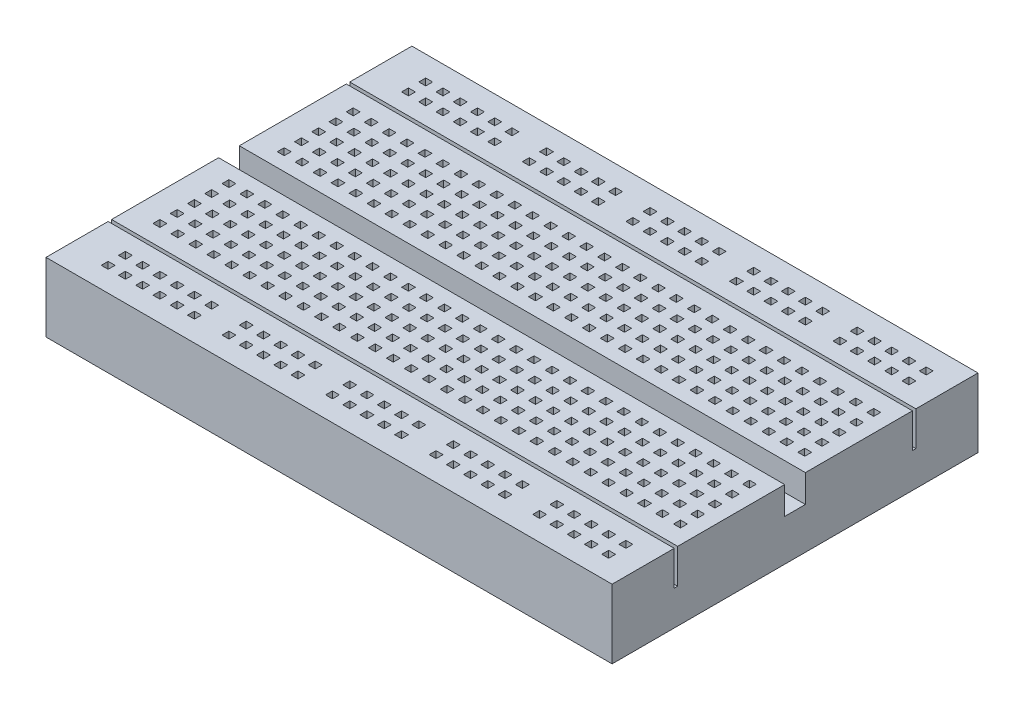
SolidWorks part; units mm, degrees
material "ABS"
ref_plane "Спереди" through (0, 0, 0) normal (0, 0, 1) x (1, 0, 0)
ref_plane "Сверху" through (0, 0, 0) normal (0, 1, 0) x (1, 0, 0)
ref_plane "Справа" through (0, 0, 0) normal (1, 0, 0) x (0, 0, -1)
sketch "Эскиз1" plane through (0, 0, 0) normal (0, 1, 0) x (1, 0, 0)
  line L1 (-41, 26.5) -> (41, 26.5)
  line L2 (-41, 26.5) -> (-41, -26.5)
  line L3 (-41, -26.5) -> (41, -26.5)
  line L4 (41, 26.5) -> (41, -26.5)
  line L5 (-41, 26.5) -> (41, -26.5) construction
  line L6 (-41, -26.5) -> (41, 26.5) construction
  point P0 (0, 0)
  dimension "D1" = 82
  dimension "D2" = 53
extrude "Бобышка-Вытянуть1" add sketch "Эскиз1" along normal blind 10
sketch "Эскиз2" plane through (0, 10, 0) normal (0, 1, 0) x (1, 0, 0)
  line L0 (41, -26.5) -> (41, 26.5) construction
  line L1 (-41, 1.5) -> (41, 1.5)
  line L2 (-41, 1.5) -> (-41, -1.5)
  line L3 (-41, -1.5) -> (41, -1.5)
  line L4 (41, 1.5) -> (41, -1.5)
  line L5 (-41, 1.5) -> (41, -1.5) construction
  line L6 (-41, -1.5) -> (41, 1.5) construction
  point P0 (0, 0)
  dimension "D1" = 3
extrude "Вырез-Вытянуть1" cut sketch "Эскиз2" against normal blind 4
sketch "Эскиз3" plane through (0, 10, 0) normal (0, 1, 0) x (1, 0, 0)
  line L0 (-41, -1.5) -> (-41, -26.5) construction
  line L1 (-36, -22.5) -> (-35, -22.5)
  line L2 (-36, -22.5) -> (-36, -23.5)
  line L3 (-36, -23.5) -> (-35, -23.5)
  line L4 (-35, -22.5) -> (-35, -23.5)
  line L5 (-41, -26.5) -> (41, -26.5) construction
  line L6 (-33.5, -22.5) -> (-32.5, -22.5)
  line L7 (-32.5, -22.5) -> (-32.5, -23.5)
  line L8 (-33.5, -23.5) -> (-32.5, -23.5)
  line L9 (-33.5, -22.5) -> (-33.5, -23.5)
  line L10 (-31, -22.5) -> (-30, -22.5)
  line L11 (-30, -22.5) -> (-30, -23.5)
  line L12 (-31, -23.5) -> (-30, -23.5)
  line L13 (-31, -22.5) -> (-31, -23.5)
  line L14 (-28.5, -22.5) -> (-27.5, -22.5)
  line L15 (-27.5, -22.5) -> (-27.5, -23.5)
  line L16 (-28.5, -23.5) -> (-27.5, -23.5)
  line L17 (-28.5, -22.5) -> (-28.5, -23.5)
  line L18 (-26, -22.5) -> (-25, -22.5)
  line L19 (-25, -22.5) -> (-25, -23.5)
  line L20 (-26, -23.5) -> (-25, -23.5)
  line L21 (-26, -22.5) -> (-26, -23.5)
  line L22 (-23.5, -22.5) -> (-22.5, -22.5)
  line L23 (-22.5, -22.5) -> (-22.5, -23.5)
  line L24 (-23.5, -23.5) -> (-22.5, -23.5)
  line L25 (-23.5, -22.5) -> (-23.5, -23.5)
  line L26 (-21, -22.5) -> (-20, -22.5) [skipped]
  line L27 (-20, -22.5) -> (-20, -23.5) [skipped]
  line L28 (-21, -23.5) -> (-20, -23.5) [skipped]
  line L29 (-21, -22.5) -> (-21, -23.5) [skipped]
  line L30 (-18.5, -22.5) -> (-17.5, -22.5)
  line L31 (-17.5, -22.5) -> (-17.5, -23.5)
  line L32 (-18.5, -23.5) -> (-17.5, -23.5)
  line L33 (-18.5, -22.5) -> (-18.5, -23.5)
  line L34 (-16, -22.5) -> (-15, -22.5)
  line L35 (-15, -22.5) -> (-15, -23.5)
  line L36 (-16, -23.5) -> (-15, -23.5)
  line L37 (-16, -22.5) -> (-16, -23.5)
  line L38 (-13.5, -22.5) -> (-12.5, -22.5)
  line L39 (-12.5, -22.5) -> (-12.5, -23.5)
  line L40 (-13.5, -23.5) -> (-12.5, -23.5)
  line L41 (-13.5, -22.5) -> (-13.5, -23.5)
  line L42 (-11, -22.5) -> (-10, -22.5)
  line L43 (-10, -22.5) -> (-10, -23.5)
  line L44 (-11, -23.5) -> (-10, -23.5)
  line L45 (-11, -22.5) -> (-11, -23.5)
  line L46 (-8.5, -22.5) -> (-7.5, -22.5)
  line L47 (-7.5, -22.5) -> (-7.5, -23.5)
  line L48 (-8.5, -23.5) -> (-7.5, -23.5)
  line L49 (-8.5, -22.5) -> (-8.5, -23.5)
  line L50 (-6, -22.5) -> (-5, -22.5) [skipped]
  line L51 (-5, -22.5) -> (-5, -23.5) [skipped]
  line L52 (-6, -23.5) -> (-5, -23.5) [skipped]
  line L53 (-6, -22.5) -> (-6, -23.5) [skipped]
  line L54 (-3.5, -22.5) -> (-2.5, -22.5)
  line L55 (-2.5, -22.5) -> (-2.5, -23.5)
  line L56 (-3.5, -23.5) -> (-2.5, -23.5)
  line L57 (-3.5, -22.5) -> (-3.5, -23.5)
  line L58 (-1, -22.5) -> (0, -22.5)
  line L59 (0, -22.5) -> (0, -23.5)
  line L60 (-1, -23.5) -> (0, -23.5)
  line L61 (-1, -22.5) -> (-1, -23.5)
  line L62 (1.5, -22.5) -> (2.5, -22.5)
  line L63 (2.5, -22.5) -> (2.5, -23.5)
  line L64 (1.5, -23.5) -> (2.5, -23.5)
  line L65 (1.5, -22.5) -> (1.5, -23.5)
  line L66 (4, -22.5) -> (5, -22.5)
  line L67 (5, -22.5) -> (5, -23.5)
  line L68 (4, -23.5) -> (5, -23.5)
  line L69 (4, -22.5) -> (4, -23.5)
  line L70 (6.5, -22.5) -> (7.5, -22.5)
  line L71 (7.5, -22.5) -> (7.5, -23.5)
  line L72 (6.5, -23.5) -> (7.5, -23.5)
  line L73 (6.5, -22.5) -> (6.5, -23.5)
  line L74 (9, -22.5) -> (10, -22.5) [skipped]
  line L75 (10, -22.5) -> (10, -23.5) [skipped]
  line L76 (9, -23.5) -> (10, -23.5) [skipped]
  line L77 (9, -22.5) -> (9, -23.5) [skipped]
  line L78 (11.5, -22.5) -> (12.5, -22.5)
  line L79 (12.5, -22.5) -> (12.5, -23.5)
  line L80 (11.5, -23.5) -> (12.5, -23.5)
  line L81 (11.5, -22.5) -> (11.5, -23.5)
  line L82 (14, -22.5) -> (15, -22.5)
  line L83 (15, -22.5) -> (15, -23.5)
  line L84 (14, -23.5) -> (15, -23.5)
  line L85 (14, -22.5) -> (14, -23.5)
  line L86 (16.5, -22.5) -> (17.5, -22.5)
  line L87 (17.5, -22.5) -> (17.5, -23.5)
  line L88 (16.5, -23.5) -> (17.5, -23.5)
  line L89 (16.5, -22.5) -> (16.5, -23.5)
  line L90 (19, -22.5) -> (20, -22.5)
  line L91 (20, -22.5) -> (20, -23.5)
  line L92 (19, -23.5) -> (20, -23.5)
  line L93 (19, -22.5) -> (19, -23.5)
  line L94 (21.5, -22.5) -> (22.5, -22.5)
  line L95 (22.5, -22.5) -> (22.5, -23.5)
  line L96 (21.5, -23.5) -> (22.5, -23.5)
  line L97 (21.5, -22.5) -> (21.5, -23.5)
  line L98 (24, -22.5) -> (25, -22.5) [skipped]
  line L99 (25, -22.5) -> (25, -23.5) [skipped]
  line L100 (24, -23.5) -> (25, -23.5) [skipped]
  line L101 (24, -22.5) -> (24, -23.5) [skipped]
  line L102 (26.5, -22.5) -> (27.5, -22.5)
  line L103 (27.5, -22.5) -> (27.5, -23.5)
  line L104 (26.5, -23.5) -> (27.5, -23.5)
  line L105 (26.5, -22.5) -> (26.5, -23.5)
  line L106 (29, -22.5) -> (30, -22.5)
  line L107 (30, -22.5) -> (30, -23.5)
  line L108 (29, -23.5) -> (30, -23.5)
  line L109 (29, -22.5) -> (29, -23.5)
  line L110 (31.5, -22.5) -> (32.5, -22.5)
  line L111 (32.5, -22.5) -> (32.5, -23.5)
  line L112 (31.5, -23.5) -> (32.5, -23.5)
  line L113 (31.5, -22.5) -> (31.5, -23.5)
  line L114 (34, -22.5) -> (35, -22.5)
  line L115 (35, -22.5) -> (35, -23.5)
  line L116 (34, -23.5) -> (35, -23.5)
  line L117 (34, -22.5) -> (34, -23.5)
  line L118 (36.5, -22.5) -> (37.5, -22.5)
  line L119 (37.5, -22.5) -> (37.5, -23.5)
  line L120 (36.5, -23.5) -> (37.5, -23.5)
  line L121 (36.5, -22.5) -> (36.5, -23.5)
  line L122 (-33.5, -20) -> (-32.5, -20)
  line L123 (-32.5, -20) -> (-32.5, -21)
  line L124 (-33.5, -21) -> (-32.5, -21)
  line L125 (-33.5, -20) -> (-33.5, -21)
  line L126 (-31, -20) -> (-30, -20)
  line L127 (-30, -20) -> (-30, -21)
  line L128 (-31, -21) -> (-30, -21)
  line L129 (-31, -20) -> (-31, -21)
  line L130 (-28.5, -20) -> (-27.5, -20)
  line L131 (-27.5, -20) -> (-27.5, -21)
  line L132 (-28.5, -21) -> (-27.5, -21)
  line L133 (-28.5, -20) -> (-28.5, -21)
  line L134 (-26, -20) -> (-25, -20)
  line L135 (-25, -20) -> (-25, -21)
  line L136 (-26, -21) -> (-25, -21)
  line L137 (-26, -20) -> (-26, -21)
  line L138 (-23.5, -20) -> (-22.5, -20)
  line L139 (-22.5, -20) -> (-22.5, -21)
  line L140 (-23.5, -21) -> (-22.5, -21)
  line L141 (-23.5, -20) -> (-23.5, -21)
  line L142 (-21, -20) -> (-20, -20) [skipped]
  line L143 (-20, -20) -> (-20, -21) [skipped]
  line L144 (-21, -21) -> (-20, -21) [skipped]
  line L145 (-21, -20) -> (-21, -21) [skipped]
  line L146 (-18.5, -20) -> (-17.5, -20)
  line L147 (-17.5, -20) -> (-17.5, -21)
  line L148 (-18.5, -21) -> (-17.5, -21)
  line L149 (-18.5, -20) -> (-18.5, -21)
  line L150 (-16, -20) -> (-15, -20)
  line L151 (-15, -20) -> (-15, -21)
  line L152 (-16, -21) -> (-15, -21)
  line L153 (-16, -20) -> (-16, -21)
  line L154 (-13.5, -20) -> (-12.5, -20)
  line L155 (-12.5, -20) -> (-12.5, -21)
  line L156 (-13.5, -21) -> (-12.5, -21)
  line L157 (-13.5, -20) -> (-13.5, -21)
  line L158 (-11, -20) -> (-10, -20)
  line L159 (-10, -20) -> (-10, -21)
  line L160 (-11, -21) -> (-10, -21)
  line L161 (-11, -20) -> (-11, -21)
  line L162 (-8.5, -20) -> (-7.5, -20)
  line L163 (-7.5, -20) -> (-7.5, -21)
  line L164 (-8.5, -21) -> (-7.5, -21)
  line L165 (-8.5, -20) -> (-8.5, -21)
  line L166 (-6, -20) -> (-5, -20) [skipped]
  line L167 (-5, -20) -> (-5, -21) [skipped]
  line L168 (-6, -21) -> (-5, -21) [skipped]
  line L169 (-6, -20) -> (-6, -21) [skipped]
  line L170 (-3.5, -20) -> (-2.5, -20)
  line L171 (-2.5, -20) -> (-2.5, -21)
  line L172 (-3.5, -21) -> (-2.5, -21)
  line L173 (-3.5, -20) -> (-3.5, -21)
  line L174 (-1, -20) -> (0, -20)
  line L175 (0, -20) -> (0, -21)
  line L176 (-1, -21) -> (0, -21)
  line L177 (-1, -20) -> (-1, -21)
  line L178 (1.5, -20) -> (2.5, -20)
  line L179 (2.5, -20) -> (2.5, -21)
  line L180 (1.5, -21) -> (2.5, -21)
  line L181 (1.5, -20) -> (1.5, -21)
  line L182 (4, -20) -> (5, -20)
  line L183 (5, -20) -> (5, -21)
  line L184 (4, -21) -> (5, -21)
  line L185 (4, -20) -> (4, -21)
  line L186 (6.5, -20) -> (7.5, -20)
  line L187 (7.5, -20) -> (7.5, -21)
  line L188 (6.5, -21) -> (7.5, -21)
  line L189 (6.5, -20) -> (6.5, -21)
  line L190 (9, -20) -> (10, -20) [skipped]
  line L191 (10, -20) -> (10, -21) [skipped]
  line L192 (9, -21) -> (10, -21) [skipped]
  line L193 (9, -20) -> (9, -21) [skipped]
  line L194 (11.5, -20) -> (12.5, -20)
  line L195 (12.5, -20) -> (12.5, -21)
  line L196 (11.5, -21) -> (12.5, -21)
  line L197 (11.5, -20) -> (11.5, -21)
  line L198 (14, -20) -> (15, -20)
  line L199 (15, -20) -> (15, -21)
  line L200 (14, -21) -> (15, -21)
  line L201 (14, -20) -> (14, -21)
  line L202 (16.5, -20) -> (17.5, -20)
  line L203 (17.5, -20) -> (17.5, -21)
  line L204 (16.5, -21) -> (17.5, -21)
  line L205 (16.5, -20) -> (16.5, -21)
  line L206 (19, -20) -> (20, -20)
  line L207 (20, -20) -> (20, -21)
  line L208 (19, -21) -> (20, -21)
  line L209 (19, -20) -> (19, -21)
  line L210 (21.5, -20) -> (22.5, -20)
  line L211 (22.5, -20) -> (22.5, -21)
  line L212 (21.5, -21) -> (22.5, -21)
  line L213 (21.5, -20) -> (21.5, -21)
  line L214 (24, -20) -> (25, -20) [skipped]
  line L215 (25, -20) -> (25, -21) [skipped]
  line L216 (24, -21) -> (25, -21) [skipped]
  line L217 (24, -20) -> (24, -21) [skipped]
  line L218 (26.5, -20) -> (27.5, -20)
  line L219 (27.5, -20) -> (27.5, -21)
  line L220 (26.5, -21) -> (27.5, -21)
  line L221 (26.5, -20) -> (26.5, -21)
  line L222 (29, -20) -> (30, -20)
  line L223 (30, -20) -> (30, -21)
  line L224 (29, -21) -> (30, -21)
  line L225 (29, -20) -> (29, -21)
  line L226 (31.5, -20) -> (32.5, -20)
  line L227 (32.5, -20) -> (32.5, -21)
  line L228 (31.5, -21) -> (32.5, -21)
  line L229 (31.5, -20) -> (31.5, -21)
  line L230 (34, -20) -> (35, -20)
  line L231 (35, -20) -> (35, -21)
  line L232 (34, -21) -> (35, -21)
  line L233 (34, -20) -> (34, -21)
  line L234 (36.5, -20) -> (37.5, -20)
  line L235 (37.5, -20) -> (37.5, -21)
  line L236 (36.5, -21) -> (37.5, -21)
  line L237 (36.5, -20) -> (36.5, -21)
  line L238 (-36, -20) -> (-35, -20)
  line L239 (-35, -20) -> (-35, -21)
  line L240 (-36, -21) -> (-35, -21)
  line L241 (-36, -20) -> (-36, -21)
  dimension "D1" = 1
  dimension "D2" = 1
  dimension "D3" = 5
  dimension "D4" = 3
  dimension "D5" = 30
  dimension "D6" = 2
extrude "Вырез-Вытянуть2" cut sketch "Эскиз3" against normal blind 5
sketch "Эскиз4" plane through (0, 10, 0) normal (0, 1, 0) x (1, 0, 0)
  line L0 (-36, -21) -> (-35, -21) construction
  line L1 (-37.5, -13.5) -> (-36.5, -13.5)
  line L2 (-37.5, -13.5) -> (-37.5, -14.5)
  line L3 (-37.5, -14.5) -> (-36.5, -14.5)
  line L4 (-36.5, -13.5) -> (-36.5, -14.5)
  line L5 (-35, -21) -> (-35, -20) construction
  line L6 (-41, -1.5) -> (-41, -26.5) construction
  line L7 (-35, -20) -> (-36, -20) construction
  line L8 (-36, -23.5) -> (-35, -23.5) construction
  line L9 (-41, -26.5) -> (41, -26.5) construction
  line L10 (-34.9, -13.5) -> (-33.9, -13.5)
  line L11 (-33.9, -13.5) -> (-33.9, -14.5)
  line L12 (-34.9, -13.5) -> (-34.9, -14.5)
  line L13 (-34.9, -14.5) -> (-33.9, -14.5)
  line L14 (-32.3, -13.5) -> (-31.3, -13.5)
  line L15 (-31.3, -13.5) -> (-31.3, -14.5)
  line L16 (-32.3, -13.5) -> (-32.3, -14.5)
  line L17 (-32.3, -14.5) -> (-31.3, -14.5)
  line L18 (-29.7, -13.5) -> (-28.7, -13.5)
  line L19 (-28.7, -13.5) -> (-28.7, -14.5)
  line L20 (-29.7, -13.5) -> (-29.7, -14.5)
  line L21 (-29.7, -14.5) -> (-28.7, -14.5)
  line L22 (-27.1, -13.5) -> (-26.1, -13.5)
  line L23 (-26.1, -13.5) -> (-26.1, -14.5)
  line L24 (-27.1, -13.5) -> (-27.1, -14.5)
  line L25 (-27.1, -14.5) -> (-26.1, -14.5)
  line L26 (-24.5, -13.5) -> (-23.5, -13.5)
  line L27 (-23.5, -13.5) -> (-23.5, -14.5)
  line L28 (-24.5, -13.5) -> (-24.5, -14.5)
  line L29 (-24.5, -14.5) -> (-23.5, -14.5)
  line L30 (-21.9, -13.5) -> (-20.9, -13.5)
  line L31 (-20.9, -13.5) -> (-20.9, -14.5)
  line L32 (-21.9, -13.5) -> (-21.9, -14.5)
  line L33 (-21.9, -14.5) -> (-20.9, -14.5)
  line L34 (-19.3, -13.5) -> (-18.3, -13.5)
  line L35 (-18.3, -13.5) -> (-18.3, -14.5)
  line L36 (-19.3, -13.5) -> (-19.3, -14.5)
  line L37 (-19.3, -14.5) -> (-18.3, -14.5)
  line L38 (-16.7, -13.5) -> (-15.7, -13.5)
  line L39 (-15.7, -13.5) -> (-15.7, -14.5)
  line L40 (-16.7, -13.5) -> (-16.7, -14.5)
  line L41 (-16.7, -14.5) -> (-15.7, -14.5)
  line L42 (-14.1, -13.5) -> (-13.1, -13.5)
  line L43 (-13.1, -13.5) -> (-13.1, -14.5)
  line L44 (-14.1, -13.5) -> (-14.1, -14.5)
  line L45 (-14.1, -14.5) -> (-13.1, -14.5)
  line L46 (-11.5, -13.5) -> (-10.5, -13.5)
  line L47 (-10.5, -13.5) -> (-10.5, -14.5)
  line L48 (-11.5, -13.5) -> (-11.5, -14.5)
  line L49 (-11.5, -14.5) -> (-10.5, -14.5)
  line L50 (-8.9, -13.5) -> (-7.9, -13.5)
  line L51 (-7.9, -13.5) -> (-7.9, -14.5)
  line L52 (-8.9, -13.5) -> (-8.9, -14.5)
  line L53 (-8.9, -14.5) -> (-7.9, -14.5)
  line L54 (-6.3, -13.5) -> (-5.3, -13.5)
  line L55 (-5.3, -13.5) -> (-5.3, -14.5)
  line L56 (-6.3, -13.5) -> (-6.3, -14.5)
  line L57 (-6.3, -14.5) -> (-5.3, -14.5)
  line L58 (-3.7, -13.5) -> (-2.7, -13.5)
  line L59 (-2.7, -13.5) -> (-2.7, -14.5)
  line L60 (-3.7, -13.5) -> (-3.7, -14.5)
  line L61 (-3.7, -14.5) -> (-2.7, -14.5)
  line L62 (-1.1, -13.5) -> (-0.1, -13.5)
  line L63 (-0.1, -13.5) -> (-0.1, -14.5)
  line L64 (-1.1, -13.5) -> (-1.1, -14.5)
  line L65 (-1.1, -14.5) -> (-0.1, -14.5)
  line L66 (1.5, -13.5) -> (2.5, -13.5)
  line L67 (2.5, -13.5) -> (2.5, -14.5)
  line L68 (1.5, -13.5) -> (1.5, -14.5)
  line L69 (1.5, -14.5) -> (2.5, -14.5)
  line L70 (4.1, -13.5) -> (5.1, -13.5)
  line L71 (5.1, -13.5) -> (5.1, -14.5)
  line L72 (4.1, -13.5) -> (4.1, -14.5)
  line L73 (4.1, -14.5) -> (5.1, -14.5)
  line L74 (6.7, -13.5) -> (7.7, -13.5)
  line L75 (7.7, -13.5) -> (7.7, -14.5)
  line L76 (6.7, -13.5) -> (6.7, -14.5)
  line L77 (6.7, -14.5) -> (7.7, -14.5)
  line L78 (9.3, -13.5) -> (10.3, -13.5)
  line L79 (10.3, -13.5) -> (10.3, -14.5)
  line L80 (9.3, -13.5) -> (9.3, -14.5)
  line L81 (9.3, -14.5) -> (10.3, -14.5)
  line L82 (11.9, -13.5) -> (12.9, -13.5)
  line L83 (12.9, -13.5) -> (12.9, -14.5)
  line L84 (11.9, -13.5) -> (11.9, -14.5)
  line L85 (11.9, -14.5) -> (12.9, -14.5)
  line L86 (14.5, -13.5) -> (15.5, -13.5)
  line L87 (15.5, -13.5) -> (15.5, -14.5)
  line L88 (14.5, -13.5) -> (14.5, -14.5)
  line L89 (14.5, -14.5) -> (15.5, -14.5)
  line L90 (17.1, -13.5) -> (18.1, -13.5)
  line L91 (18.1, -13.5) -> (18.1, -14.5)
  line L92 (17.1, -13.5) -> (17.1, -14.5)
  line L93 (17.1, -14.5) -> (18.1, -14.5)
  line L94 (19.7, -13.5) -> (20.7, -13.5)
  line L95 (20.7, -13.5) -> (20.7, -14.5)
  line L96 (19.7, -13.5) -> (19.7, -14.5)
  line L97 (19.7, -14.5) -> (20.7, -14.5)
  line L98 (22.3, -13.5) -> (23.3, -13.5)
  line L99 (23.3, -13.5) -> (23.3, -14.5)
  line L100 (22.3, -13.5) -> (22.3, -14.5)
  line L101 (22.3, -14.5) -> (23.3, -14.5)
  line L102 (24.9, -13.5) -> (25.9, -13.5)
  line L103 (25.9, -13.5) -> (25.9, -14.5)
  line L104 (24.9, -13.5) -> (24.9, -14.5)
  line L105 (24.9, -14.5) -> (25.9, -14.5)
  line L106 (27.5, -13.5) -> (28.5, -13.5)
  line L107 (28.5, -13.5) -> (28.5, -14.5)
  line L108 (27.5, -13.5) -> (27.5, -14.5)
  line L109 (27.5, -14.5) -> (28.5, -14.5)
  line L110 (30.1, -13.5) -> (31.1, -13.5)
  line L111 (31.1, -13.5) -> (31.1, -14.5)
  line L112 (30.1, -13.5) -> (30.1, -14.5)
  line L113 (30.1, -14.5) -> (31.1, -14.5)
  line L114 (32.7, -13.5) -> (33.7, -13.5)
  line L115 (33.7, -13.5) -> (33.7, -14.5)
  line L116 (32.7, -13.5) -> (32.7, -14.5)
  line L117 (32.7, -14.5) -> (33.7, -14.5)
  line L118 (35.3, -13.5) -> (36.3, -13.5)
  line L119 (36.3, -13.5) -> (36.3, -14.5)
  line L120 (35.3, -13.5) -> (35.3, -14.5)
  line L121 (35.3, -14.5) -> (36.3, -14.5)
  line L122 (37.9, -13.5) -> (38.9, -13.5)
  line L123 (38.9, -13.5) -> (38.9, -14.5)
  line L124 (37.9, -13.5) -> (37.9, -14.5)
  line L125 (37.9, -14.5) -> (38.9, -14.5)
  line L126 (-34.9, -11) -> (-33.9, -11)
  line L127 (-33.9, -11) -> (-33.9, -12)
  line L128 (-34.9, -11) -> (-34.9, -12)
  line L129 (-34.9, -12) -> (-33.9, -12)
  line L130 (-32.3, -11) -> (-31.3, -11)
  line L131 (-31.3, -11) -> (-31.3, -12)
  line L132 (-32.3, -11) -> (-32.3, -12)
  line L133 (-32.3, -12) -> (-31.3, -12)
  line L134 (-29.7, -11) -> (-28.7, -11)
  line L135 (-28.7, -11) -> (-28.7, -12)
  line L136 (-29.7, -11) -> (-29.7, -12)
  line L137 (-29.7, -12) -> (-28.7, -12)
  line L138 (-27.1, -11) -> (-26.1, -11)
  line L139 (-26.1, -11) -> (-26.1, -12)
  line L140 (-27.1, -11) -> (-27.1, -12)
  line L141 (-27.1, -12) -> (-26.1, -12)
  line L142 (-24.5, -11) -> (-23.5, -11)
  line L143 (-23.5, -11) -> (-23.5, -12)
  line L144 (-24.5, -11) -> (-24.5, -12)
  line L145 (-24.5, -12) -> (-23.5, -12)
  line L146 (-21.9, -11) -> (-20.9, -11)
  line L147 (-20.9, -11) -> (-20.9, -12)
  line L148 (-21.9, -11) -> (-21.9, -12)
  line L149 (-21.9, -12) -> (-20.9, -12)
  line L150 (-19.3, -11) -> (-18.3, -11)
  line L151 (-18.3, -11) -> (-18.3, -12)
  line L152 (-19.3, -11) -> (-19.3, -12)
  line L153 (-19.3, -12) -> (-18.3, -12)
  line L154 (-16.7, -11) -> (-15.7, -11)
  line L155 (-15.7, -11) -> (-15.7, -12)
  line L156 (-16.7, -11) -> (-16.7, -12)
  line L157 (-16.7, -12) -> (-15.7, -12)
  line L158 (-14.1, -11) -> (-13.1, -11)
  line L159 (-13.1, -11) -> (-13.1, -12)
  line L160 (-14.1, -11) -> (-14.1, -12)
  line L161 (-14.1, -12) -> (-13.1, -12)
  line L162 (-11.5, -11) -> (-10.5, -11)
  line L163 (-10.5, -11) -> (-10.5, -12)
  line L164 (-11.5, -11) -> (-11.5, -12)
  line L165 (-11.5, -12) -> (-10.5, -12)
  line L166 (-8.9, -11) -> (-7.9, -11)
  line L167 (-7.9, -11) -> (-7.9, -12)
  line L168 (-8.9, -11) -> (-8.9, -12)
  line L169 (-8.9, -12) -> (-7.9, -12)
  line L170 (-6.3, -11) -> (-5.3, -11)
  line L171 (-5.3, -11) -> (-5.3, -12)
  line L172 (-6.3, -11) -> (-6.3, -12)
  line L173 (-6.3, -12) -> (-5.3, -12)
  line L174 (-3.7, -11) -> (-2.7, -11)
  line L175 (-2.7, -11) -> (-2.7, -12)
  line L176 (-3.7, -11) -> (-3.7, -12)
  line L177 (-3.7, -12) -> (-2.7, -12)
  line L178 (-1.1, -11) -> (-0.1, -11)
  line L179 (-0.1, -11) -> (-0.1, -12)
  line L180 (-1.1, -11) -> (-1.1, -12)
  line L181 (-1.1, -12) -> (-0.1, -12)
  line L182 (1.5, -11) -> (2.5, -11)
  line L183 (2.5, -11) -> (2.5, -12)
  line L184 (1.5, -11) -> (1.5, -12)
  line L185 (1.5, -12) -> (2.5, -12)
  line L186 (4.1, -11) -> (5.1, -11)
  line L187 (5.1, -11) -> (5.1, -12)
  line L188 (4.1, -11) -> (4.1, -12)
  line L189 (4.1, -12) -> (5.1, -12)
  line L190 (6.7, -11) -> (7.7, -11)
  line L191 (7.7, -11) -> (7.7, -12)
  line L192 (6.7, -11) -> (6.7, -12)
  line L193 (6.7, -12) -> (7.7, -12)
  line L194 (9.3, -11) -> (10.3, -11)
  line L195 (10.3, -11) -> (10.3, -12)
  line L196 (9.3, -11) -> (9.3, -12)
  line L197 (9.3, -12) -> (10.3, -12)
  line L198 (11.9, -11) -> (12.9, -11)
  line L199 (12.9, -11) -> (12.9, -12)
  line L200 (11.9, -11) -> (11.9, -12)
  line L201 (11.9, -12) -> (12.9, -12)
  line L202 (14.5, -11) -> (15.5, -11)
  line L203 (15.5, -11) -> (15.5, -12)
  line L204 (14.5, -11) -> (14.5, -12)
  line L205 (14.5, -12) -> (15.5, -12)
  line L206 (17.1, -11) -> (18.1, -11)
  line L207 (18.1, -11) -> (18.1, -12)
  line L208 (17.1, -11) -> (17.1, -12)
  line L209 (17.1, -12) -> (18.1, -12)
  line L210 (19.7, -11) -> (20.7, -11)
  line L211 (20.7, -11) -> (20.7, -12)
  line L212 (19.7, -11) -> (19.7, -12)
  line L213 (19.7, -12) -> (20.7, -12)
  line L214 (22.3, -11) -> (23.3, -11)
  line L215 (23.3, -11) -> (23.3, -12)
  line L216 (22.3, -11) -> (22.3, -12)
  line L217 (22.3, -12) -> (23.3, -12)
  line L218 (24.9, -11) -> (25.9, -11)
  line L219 (25.9, -11) -> (25.9, -12)
  line L220 (24.9, -11) -> (24.9, -12)
  line L221 (24.9, -12) -> (25.9, -12)
  line L222 (27.5, -11) -> (28.5, -11)
  line L223 (28.5, -11) -> (28.5, -12)
  line L224 (27.5, -11) -> (27.5, -12)
  line L225 (27.5, -12) -> (28.5, -12)
  line L226 (30.1, -11) -> (31.1, -11)
  line L227 (31.1, -11) -> (31.1, -12)
  line L228 (30.1, -11) -> (30.1, -12)
  line L229 (30.1, -12) -> (31.1, -12)
  line L230 (32.7, -11) -> (33.7, -11)
  line L231 (33.7, -11) -> (33.7, -12)
  line L232 (32.7, -11) -> (32.7, -12)
  line L233 (32.7, -12) -> (33.7, -12)
  line L234 (35.3, -11) -> (36.3, -11)
  line L235 (36.3, -11) -> (36.3, -12)
  line L236 (35.3, -11) -> (35.3, -12)
  line L237 (35.3, -12) -> (36.3, -12)
  line L238 (37.9, -11) -> (38.9, -11)
  line L239 (38.9, -11) -> (38.9, -12)
  line L240 (37.9, -11) -> (37.9, -12)
  line L241 (37.9, -12) -> (38.9, -12)
  line L242 (-34.9, -8.5) -> (-33.9, -8.5)
  line L243 (-33.9, -8.5) -> (-33.9, -9.5)
  line L244 (-34.9, -8.5) -> (-34.9, -9.5)
  line L245 (-34.9, -9.5) -> (-33.9, -9.5)
  line L246 (-32.3, -8.5) -> (-31.3, -8.5)
  line L247 (-31.3, -8.5) -> (-31.3, -9.5)
  line L248 (-32.3, -8.5) -> (-32.3, -9.5)
  line L249 (-32.3, -9.5) -> (-31.3, -9.5)
  line L250 (-29.7, -8.5) -> (-28.7, -8.5)
  line L251 (-28.7, -8.5) -> (-28.7, -9.5)
  line L252 (-29.7, -8.5) -> (-29.7, -9.5)
  line L253 (-29.7, -9.5) -> (-28.7, -9.5)
  line L254 (-27.1, -8.5) -> (-26.1, -8.5)
  line L255 (-26.1, -8.5) -> (-26.1, -9.5)
  line L256 (-27.1, -8.5) -> (-27.1, -9.5)
  line L257 (-27.1, -9.5) -> (-26.1, -9.5)
  line L258 (-24.5, -8.5) -> (-23.5, -8.5)
  line L259 (-23.5, -8.5) -> (-23.5, -9.5)
  line L260 (-24.5, -8.5) -> (-24.5, -9.5)
  line L261 (-24.5, -9.5) -> (-23.5, -9.5)
  line L262 (-21.9, -8.5) -> (-20.9, -8.5)
  line L263 (-20.9, -8.5) -> (-20.9, -9.5)
  line L264 (-21.9, -8.5) -> (-21.9, -9.5)
  line L265 (-21.9, -9.5) -> (-20.9, -9.5)
  line L266 (-19.3, -8.5) -> (-18.3, -8.5)
  line L267 (-18.3, -8.5) -> (-18.3, -9.5)
  line L268 (-19.3, -8.5) -> (-19.3, -9.5)
  line L269 (-19.3, -9.5) -> (-18.3, -9.5)
  line L270 (-16.7, -8.5) -> (-15.7, -8.5)
  line L271 (-15.7, -8.5) -> (-15.7, -9.5)
  line L272 (-16.7, -8.5) -> (-16.7, -9.5)
  line L273 (-16.7, -9.5) -> (-15.7, -9.5)
  line L274 (-14.1, -8.5) -> (-13.1, -8.5)
  line L275 (-13.1, -8.5) -> (-13.1, -9.5)
  line L276 (-14.1, -8.5) -> (-14.1, -9.5)
  line L277 (-14.1, -9.5) -> (-13.1, -9.5)
  line L278 (-11.5, -8.5) -> (-10.5, -8.5)
  line L279 (-10.5, -8.5) -> (-10.5, -9.5)
  line L280 (-11.5, -8.5) -> (-11.5, -9.5)
  line L281 (-11.5, -9.5) -> (-10.5, -9.5)
  line L282 (-8.9, -8.5) -> (-7.9, -8.5)
  line L283 (-7.9, -8.5) -> (-7.9, -9.5)
  line L284 (-8.9, -8.5) -> (-8.9, -9.5)
  line L285 (-8.9, -9.5) -> (-7.9, -9.5)
  line L286 (-6.3, -8.5) -> (-5.3, -8.5)
  line L287 (-5.3, -8.5) -> (-5.3, -9.5)
  line L288 (-6.3, -8.5) -> (-6.3, -9.5)
  line L289 (-6.3, -9.5) -> (-5.3, -9.5)
  line L290 (-3.7, -8.5) -> (-2.7, -8.5)
  line L291 (-2.7, -8.5) -> (-2.7, -9.5)
  line L292 (-3.7, -8.5) -> (-3.7, -9.5)
  line L293 (-3.7, -9.5) -> (-2.7, -9.5)
  line L294 (-1.1, -8.5) -> (-0.1, -8.5)
  line L295 (-0.1, -8.5) -> (-0.1, -9.5)
  line L296 (-1.1, -8.5) -> (-1.1, -9.5)
  line L297 (-1.1, -9.5) -> (-0.1, -9.5)
  line L298 (1.5, -8.5) -> (2.5, -8.5)
  line L299 (2.5, -8.5) -> (2.5, -9.5)
  line L300 (1.5, -8.5) -> (1.5, -9.5)
  line L301 (1.5, -9.5) -> (2.5, -9.5)
  line L302 (4.1, -8.5) -> (5.1, -8.5)
  line L303 (5.1, -8.5) -> (5.1, -9.5)
  line L304 (4.1, -8.5) -> (4.1, -9.5)
  line L305 (4.1, -9.5) -> (5.1, -9.5)
  line L306 (6.7, -8.5) -> (7.7, -8.5)
  line L307 (7.7, -8.5) -> (7.7, -9.5)
  line L308 (6.7, -8.5) -> (6.7, -9.5)
  line L309 (6.7, -9.5) -> (7.7, -9.5)
  line L310 (9.3, -8.5) -> (10.3, -8.5)
  line L311 (10.3, -8.5) -> (10.3, -9.5)
  line L312 (9.3, -8.5) -> (9.3, -9.5)
  line L313 (9.3, -9.5) -> (10.3, -9.5)
  line L314 (11.9, -8.5) -> (12.9, -8.5)
  line L315 (12.9, -8.5) -> (12.9, -9.5)
  line L316 (11.9, -8.5) -> (11.9, -9.5)
  line L317 (11.9, -9.5) -> (12.9, -9.5)
  line L318 (14.5, -8.5) -> (15.5, -8.5)
  line L319 (15.5, -8.5) -> (15.5, -9.5)
  line L320 (14.5, -8.5) -> (14.5, -9.5)
  line L321 (14.5, -9.5) -> (15.5, -9.5)
  line L322 (17.1, -8.5) -> (18.1, -8.5)
  line L323 (18.1, -8.5) -> (18.1, -9.5)
  line L324 (17.1, -8.5) -> (17.1, -9.5)
  line L325 (17.1, -9.5) -> (18.1, -9.5)
  line L326 (19.7, -8.5) -> (20.7, -8.5)
  line L327 (20.7, -8.5) -> (20.7, -9.5)
  line L328 (19.7, -8.5) -> (19.7, -9.5)
  line L329 (19.7, -9.5) -> (20.7, -9.5)
  line L330 (22.3, -8.5) -> (23.3, -8.5)
  line L331 (23.3, -8.5) -> (23.3, -9.5)
  line L332 (22.3, -8.5) -> (22.3, -9.5)
  line L333 (22.3, -9.5) -> (23.3, -9.5)
  line L334 (24.9, -8.5) -> (25.9, -8.5)
  line L335 (25.9, -8.5) -> (25.9, -9.5)
  line L336 (24.9, -8.5) -> (24.9, -9.5)
  line L337 (24.9, -9.5) -> (25.9, -9.5)
  line L338 (27.5, -8.5) -> (28.5, -8.5)
  line L339 (28.5, -8.5) -> (28.5, -9.5)
  line L340 (27.5, -8.5) -> (27.5, -9.5)
  line L341 (27.5, -9.5) -> (28.5, -9.5)
  line L342 (30.1, -8.5) -> (31.1, -8.5)
  line L343 (31.1, -8.5) -> (31.1, -9.5)
  line L344 (30.1, -8.5) -> (30.1, -9.5)
  line L345 (30.1, -9.5) -> (31.1, -9.5)
  line L346 (32.7, -8.5) -> (33.7, -8.5)
  line L347 (33.7, -8.5) -> (33.7, -9.5)
  line L348 (32.7, -8.5) -> (32.7, -9.5)
  line L349 (32.7, -9.5) -> (33.7, -9.5)
  line L350 (35.3, -8.5) -> (36.3, -8.5)
  line L351 (36.3, -8.5) -> (36.3, -9.5)
  line L352 (35.3, -8.5) -> (35.3, -9.5)
  line L353 (35.3, -9.5) -> (36.3, -9.5)
  line L354 (37.9, -8.5) -> (38.9, -8.5)
  line L355 (38.9, -8.5) -> (38.9, -9.5)
  line L356 (37.9, -8.5) -> (37.9, -9.5)
  line L357 (37.9, -9.5) -> (38.9, -9.5)
  line L358 (-34.9, -6) -> (-33.9, -6)
  line L359 (-33.9, -6) -> (-33.9, -7)
  line L360 (-34.9, -6) -> (-34.9, -7)
  line L361 (-34.9, -7) -> (-33.9, -7)
  line L362 (-32.3, -6) -> (-31.3, -6)
  line L363 (-31.3, -6) -> (-31.3, -7)
  line L364 (-32.3, -6) -> (-32.3, -7)
  line L365 (-32.3, -7) -> (-31.3, -7)
  line L366 (-29.7, -6) -> (-28.7, -6)
  line L367 (-28.7, -6) -> (-28.7, -7)
  line L368 (-29.7, -6) -> (-29.7, -7)
  line L369 (-29.7, -7) -> (-28.7, -7)
  line L370 (-27.1, -6) -> (-26.1, -6)
  line L371 (-26.1, -6) -> (-26.1, -7)
  line L372 (-27.1, -6) -> (-27.1, -7)
  line L373 (-27.1, -7) -> (-26.1, -7)
  line L374 (-24.5, -6) -> (-23.5, -6)
  line L375 (-23.5, -6) -> (-23.5, -7)
  line L376 (-24.5, -6) -> (-24.5, -7)
  line L377 (-24.5, -7) -> (-23.5, -7)
  line L378 (-21.9, -6) -> (-20.9, -6)
  line L379 (-20.9, -6) -> (-20.9, -7)
  line L380 (-21.9, -6) -> (-21.9, -7)
  line L381 (-21.9, -7) -> (-20.9, -7)
  line L382 (-19.3, -6) -> (-18.3, -6)
  line L383 (-18.3, -6) -> (-18.3, -7)
  line L384 (-19.3, -6) -> (-19.3, -7)
  line L385 (-19.3, -7) -> (-18.3, -7)
  line L386 (-16.7, -6) -> (-15.7, -6)
  line L387 (-15.7, -6) -> (-15.7, -7)
  line L388 (-16.7, -6) -> (-16.7, -7)
  line L389 (-16.7, -7) -> (-15.7, -7)
  line L390 (-14.1, -6) -> (-13.1, -6)
  line L391 (-13.1, -6) -> (-13.1, -7)
  line L392 (-14.1, -6) -> (-14.1, -7)
  line L393 (-14.1, -7) -> (-13.1, -7)
  line L394 (-11.5, -6) -> (-10.5, -6)
  line L395 (-10.5, -6) -> (-10.5, -7)
  line L396 (-11.5, -6) -> (-11.5, -7)
  line L397 (-11.5, -7) -> (-10.5, -7)
  line L398 (-8.9, -6) -> (-7.9, -6)
  line L399 (-7.9, -6) -> (-7.9, -7)
  line L400 (-8.9, -6) -> (-8.9, -7)
  line L401 (-8.9, -7) -> (-7.9, -7)
  line L402 (-6.3, -6) -> (-5.3, -6)
  line L403 (-5.3, -6) -> (-5.3, -7)
  line L404 (-6.3, -6) -> (-6.3, -7)
  line L405 (-6.3, -7) -> (-5.3, -7)
  line L406 (-3.7, -6) -> (-2.7, -6)
  line L407 (-2.7, -6) -> (-2.7, -7)
  line L408 (-3.7, -6) -> (-3.7, -7)
  line L409 (-3.7, -7) -> (-2.7, -7)
  line L410 (-1.1, -6) -> (-0.1, -6)
  line L411 (-0.1, -6) -> (-0.1, -7)
  line L412 (-1.1, -6) -> (-1.1, -7)
  line L413 (-1.1, -7) -> (-0.1, -7)
  line L414 (1.5, -6) -> (2.5, -6)
  line L415 (2.5, -6) -> (2.5, -7)
  line L416 (1.5, -6) -> (1.5, -7)
  line L417 (1.5, -7) -> (2.5, -7)
  line L418 (4.1, -6) -> (5.1, -6)
  line L419 (5.1, -6) -> (5.1, -7)
  line L420 (4.1, -6) -> (4.1, -7)
  line L421 (4.1, -7) -> (5.1, -7)
  line L422 (6.7, -6) -> (7.7, -6)
  line L423 (7.7, -6) -> (7.7, -7)
  line L424 (6.7, -6) -> (6.7, -7)
  line L425 (6.7, -7) -> (7.7, -7)
  line L426 (9.3, -6) -> (10.3, -6)
  line L427 (10.3, -6) -> (10.3, -7)
  line L428 (9.3, -6) -> (9.3, -7)
  line L429 (9.3, -7) -> (10.3, -7)
  line L430 (11.9, -6) -> (12.9, -6)
  line L431 (12.9, -6) -> (12.9, -7)
  line L432 (11.9, -6) -> (11.9, -7)
  line L433 (11.9, -7) -> (12.9, -7)
  line L434 (14.5, -6) -> (15.5, -6)
  line L435 (15.5, -6) -> (15.5, -7)
  line L436 (14.5, -6) -> (14.5, -7)
  line L437 (14.5, -7) -> (15.5, -7)
  line L438 (17.1, -6) -> (18.1, -6)
  line L439 (18.1, -6) -> (18.1, -7)
  line L440 (17.1, -6) -> (17.1, -7)
  line L441 (17.1, -7) -> (18.1, -7)
  line L442 (19.7, -6) -> (20.7, -6)
  line L443 (20.7, -6) -> (20.7, -7)
  line L444 (19.7, -6) -> (19.7, -7)
  line L445 (19.7, -7) -> (20.7, -7)
  line L446 (22.3, -6) -> (23.3, -6)
  line L447 (23.3, -6) -> (23.3, -7)
  line L448 (22.3, -6) -> (22.3, -7)
  line L449 (22.3, -7) -> (23.3, -7)
  line L450 (24.9, -6) -> (25.9, -6)
  line L451 (25.9, -6) -> (25.9, -7)
  line L452 (24.9, -6) -> (24.9, -7)
  line L453 (24.9, -7) -> (25.9, -7)
  line L454 (27.5, -6) -> (28.5, -6)
  line L455 (28.5, -6) -> (28.5, -7)
  line L456 (27.5, -6) -> (27.5, -7)
  line L457 (27.5, -7) -> (28.5, -7)
  line L458 (30.1, -6) -> (31.1, -6)
  line L459 (31.1, -6) -> (31.1, -7)
  line L460 (30.1, -6) -> (30.1, -7)
  line L461 (30.1, -7) -> (31.1, -7)
  line L462 (32.7, -6) -> (33.7, -6)
  line L463 (33.7, -6) -> (33.7, -7)
  line L464 (32.7, -6) -> (32.7, -7)
  line L465 (32.7, -7) -> (33.7, -7)
  line L466 (35.3, -6) -> (36.3, -6)
  line L467 (36.3, -6) -> (36.3, -7)
  line L468 (35.3, -6) -> (35.3, -7)
  line L469 (35.3, -7) -> (36.3, -7)
  line L470 (37.9, -6) -> (38.9, -6)
  line L471 (38.9, -6) -> (38.9, -7)
  line L472 (37.9, -6) -> (37.9, -7)
  line L473 (37.9, -7) -> (38.9, -7)
  line L474 (-34.9, -3.5) -> (-33.9, -3.5)
  line L475 (-33.9, -3.5) -> (-33.9, -4.5)
  line L476 (-34.9, -3.5) -> (-34.9, -4.5)
  line L477 (-34.9, -4.5) -> (-33.9, -4.5)
  line L478 (-32.3, -3.5) -> (-31.3, -3.5)
  line L479 (-31.3, -3.5) -> (-31.3, -4.5)
  line L480 (-32.3, -3.5) -> (-32.3, -4.5)
  line L481 (-32.3, -4.5) -> (-31.3, -4.5)
  line L482 (-29.7, -3.5) -> (-28.7, -3.5)
  line L483 (-28.7, -3.5) -> (-28.7, -4.5)
  line L484 (-29.7, -3.5) -> (-29.7, -4.5)
  line L485 (-29.7, -4.5) -> (-28.7, -4.5)
  line L486 (-27.1, -3.5) -> (-26.1, -3.5)
  line L487 (-26.1, -3.5) -> (-26.1, -4.5)
  line L488 (-27.1, -3.5) -> (-27.1, -4.5)
  line L489 (-27.1, -4.5) -> (-26.1, -4.5)
  line L490 (-24.5, -3.5) -> (-23.5, -3.5)
  line L491 (-23.5, -3.5) -> (-23.5, -4.5)
  line L492 (-24.5, -3.5) -> (-24.5, -4.5)
  line L493 (-24.5, -4.5) -> (-23.5, -4.5)
  line L494 (-21.9, -3.5) -> (-20.9, -3.5)
  line L495 (-20.9, -3.5) -> (-20.9, -4.5)
  line L496 (-21.9, -3.5) -> (-21.9, -4.5)
  line L497 (-21.9, -4.5) -> (-20.9, -4.5)
  line L498 (-19.3, -3.5) -> (-18.3, -3.5)
  line L499 (-18.3, -3.5) -> (-18.3, -4.5)
  line L500 (-19.3, -3.5) -> (-19.3, -4.5)
  line L501 (-19.3, -4.5) -> (-18.3, -4.5)
  line L502 (-16.7, -3.5) -> (-15.7, -3.5)
  line L503 (-15.7, -3.5) -> (-15.7, -4.5)
  line L504 (-16.7, -3.5) -> (-16.7, -4.5)
  line L505 (-16.7, -4.5) -> (-15.7, -4.5)
  line L506 (-14.1, -3.5) -> (-13.1, -3.5)
  line L507 (-13.1, -3.5) -> (-13.1, -4.5)
  line L508 (-14.1, -3.5) -> (-14.1, -4.5)
  line L509 (-14.1, -4.5) -> (-13.1, -4.5)
  line L510 (-11.5, -3.5) -> (-10.5, -3.5)
  line L511 (-10.5, -3.5) -> (-10.5, -4.5)
  line L512 (-11.5, -3.5) -> (-11.5, -4.5)
  line L513 (-11.5, -4.5) -> (-10.5, -4.5)
  line L514 (-8.9, -3.5) -> (-7.9, -3.5)
  line L515 (-7.9, -3.5) -> (-7.9, -4.5)
  line L516 (-8.9, -3.5) -> (-8.9, -4.5)
  line L517 (-8.9, -4.5) -> (-7.9, -4.5)
  line L518 (-6.3, -3.5) -> (-5.3, -3.5)
  line L519 (-5.3, -3.5) -> (-5.3, -4.5)
  line L520 (-6.3, -3.5) -> (-6.3, -4.5)
  line L521 (-6.3, -4.5) -> (-5.3, -4.5)
  line L522 (-3.7, -3.5) -> (-2.7, -3.5)
  line L523 (-2.7, -3.5) -> (-2.7, -4.5)
  line L524 (-3.7, -3.5) -> (-3.7, -4.5)
  line L525 (-3.7, -4.5) -> (-2.7, -4.5)
  line L526 (-1.1, -3.5) -> (-0.1, -3.5)
  line L527 (-0.1, -3.5) -> (-0.1, -4.5)
  line L528 (-1.1, -3.5) -> (-1.1, -4.5)
  line L529 (-1.1, -4.5) -> (-0.1, -4.5)
  line L530 (1.5, -3.5) -> (2.5, -3.5)
  line L531 (2.5, -3.5) -> (2.5, -4.5)
  line L532 (1.5, -3.5) -> (1.5, -4.5)
  line L533 (1.5, -4.5) -> (2.5, -4.5)
  line L534 (4.1, -3.5) -> (5.1, -3.5)
  line L535 (5.1, -3.5) -> (5.1, -4.5)
  line L536 (4.1, -3.5) -> (4.1, -4.5)
  line L537 (4.1, -4.5) -> (5.1, -4.5)
  line L538 (6.7, -3.5) -> (7.7, -3.5)
  line L539 (7.7, -3.5) -> (7.7, -4.5)
  line L540 (6.7, -3.5) -> (6.7, -4.5)
  line L541 (6.7, -4.5) -> (7.7, -4.5)
  line L542 (9.3, -3.5) -> (10.3, -3.5)
  line L543 (10.3, -3.5) -> (10.3, -4.5)
  line L544 (9.3, -3.5) -> (9.3, -4.5)
  line L545 (9.3, -4.5) -> (10.3, -4.5)
  line L546 (11.9, -3.5) -> (12.9, -3.5)
  line L547 (12.9, -3.5) -> (12.9, -4.5)
  line L548 (11.9, -3.5) -> (11.9, -4.5)
  line L549 (11.9, -4.5) -> (12.9, -4.5)
  line L550 (14.5, -3.5) -> (15.5, -3.5)
  line L551 (15.5, -3.5) -> (15.5, -4.5)
  line L552 (14.5, -3.5) -> (14.5, -4.5)
  line L553 (14.5, -4.5) -> (15.5, -4.5)
  line L554 (17.1, -3.5) -> (18.1, -3.5)
  line L555 (18.1, -3.5) -> (18.1, -4.5)
  line L556 (17.1, -3.5) -> (17.1, -4.5)
  line L557 (17.1, -4.5) -> (18.1, -4.5)
  line L558 (19.7, -3.5) -> (20.7, -3.5)
  line L559 (20.7, -3.5) -> (20.7, -4.5)
  line L560 (19.7, -3.5) -> (19.7, -4.5)
  line L561 (19.7, -4.5) -> (20.7, -4.5)
  line L562 (22.3, -3.5) -> (23.3, -3.5)
  line L563 (23.3, -3.5) -> (23.3, -4.5)
  line L564 (22.3, -3.5) -> (22.3, -4.5)
  line L565 (22.3, -4.5) -> (23.3, -4.5)
  line L566 (24.9, -3.5) -> (25.9, -3.5)
  line L567 (25.9, -3.5) -> (25.9, -4.5)
  line L568 (24.9, -3.5) -> (24.9, -4.5)
  line L569 (24.9, -4.5) -> (25.9, -4.5)
  line L570 (27.5, -3.5) -> (28.5, -3.5)
  line L571 (28.5, -3.5) -> (28.5, -4.5)
  line L572 (27.5, -3.5) -> (27.5, -4.5)
  line L573 (27.5, -4.5) -> (28.5, -4.5)
  line L574 (30.1, -3.5) -> (31.1, -3.5)
  line L575 (31.1, -3.5) -> (31.1, -4.5)
  line L576 (30.1, -3.5) -> (30.1, -4.5)
  line L577 (30.1, -4.5) -> (31.1, -4.5)
  line L578 (32.7, -3.5) -> (33.7, -3.5)
  line L579 (33.7, -3.5) -> (33.7, -4.5)
  line L580 (32.7, -3.5) -> (32.7, -4.5)
  line L581 (32.7, -4.5) -> (33.7, -4.5)
  line L582 (35.3, -3.5) -> (36.3, -3.5)
  line L583 (36.3, -3.5) -> (36.3, -4.5)
  line L584 (35.3, -3.5) -> (35.3, -4.5)
  line L585 (35.3, -4.5) -> (36.3, -4.5)
  line L586 (37.9, -3.5) -> (38.9, -3.5)
  line L587 (38.9, -3.5) -> (38.9, -4.5)
  line L588 (37.9, -3.5) -> (37.9, -4.5)
  line L589 (37.9, -4.5) -> (38.9, -4.5)
  line L590 (-37.5, -11) -> (-36.5, -11)
  line L591 (-36.5, -11) -> (-36.5, -12)
  line L592 (-37.5, -11) -> (-37.5, -12)
  line L593 (-37.5, -12) -> (-36.5, -12)
  line L594 (-37.5, -8.5) -> (-36.5, -8.5)
  line L595 (-36.5, -8.5) -> (-36.5, -9.5)
  line L596 (-37.5, -8.5) -> (-37.5, -9.5)
  line L597 (-37.5, -9.5) -> (-36.5, -9.5)
  line L598 (-37.5, -6) -> (-36.5, -6)
  line L599 (-36.5, -6) -> (-36.5, -7)
  line L600 (-37.5, -6) -> (-37.5, -7)
  line L601 (-37.5, -7) -> (-36.5, -7)
  line L602 (-37.5, -3.5) -> (-36.5, -3.5)
  line L603 (-36.5, -3.5) -> (-36.5, -4.5)
  line L604 (-37.5, -3.5) -> (-37.5, -4.5)
  line L605 (-37.5, -4.5) -> (-36.5, -4.5)
  dimension "D1" = 3.5
  dimension "D2" = 12
  dimension "D3" = 30
  dimension "D4" = 5
extrude "Вырез-Вытянуть3" cut sketch "Эскиз4" against normal blind 5
sketch "Эскиз5" plane through (0, 10, 0) normal (0, 1, 0) x (1, 0, 0)
  line L0 (-41, -1.5) -> (-41, -26.5) construction
  line L1 (-41, -17.5) -> (41, -17.5)
  line L2 (-41, -17.5) -> (-41, -17)
  line L3 (-41, -17) -> (41, -17)
  line L4 (41, -17.5) -> (41, -17)
  line L5 (41, -26.5) -> (41, -1.5) construction
  line L6 (-41, -26.5) -> (41, -26.5) construction
  dimension "D1" = 9
  dimension "D2" = 0.5
extrude "Вырез-Вытянуть4" cut sketch "Эскиз5" against normal blind 5
mirror "Зеркальное отражение2" about plane through (0, 0, 0) normal (0, 0, 1) of "Вырез-Вытянуть4", "Вырез-Вытянуть2", "Вырез-Вытянуть3"
